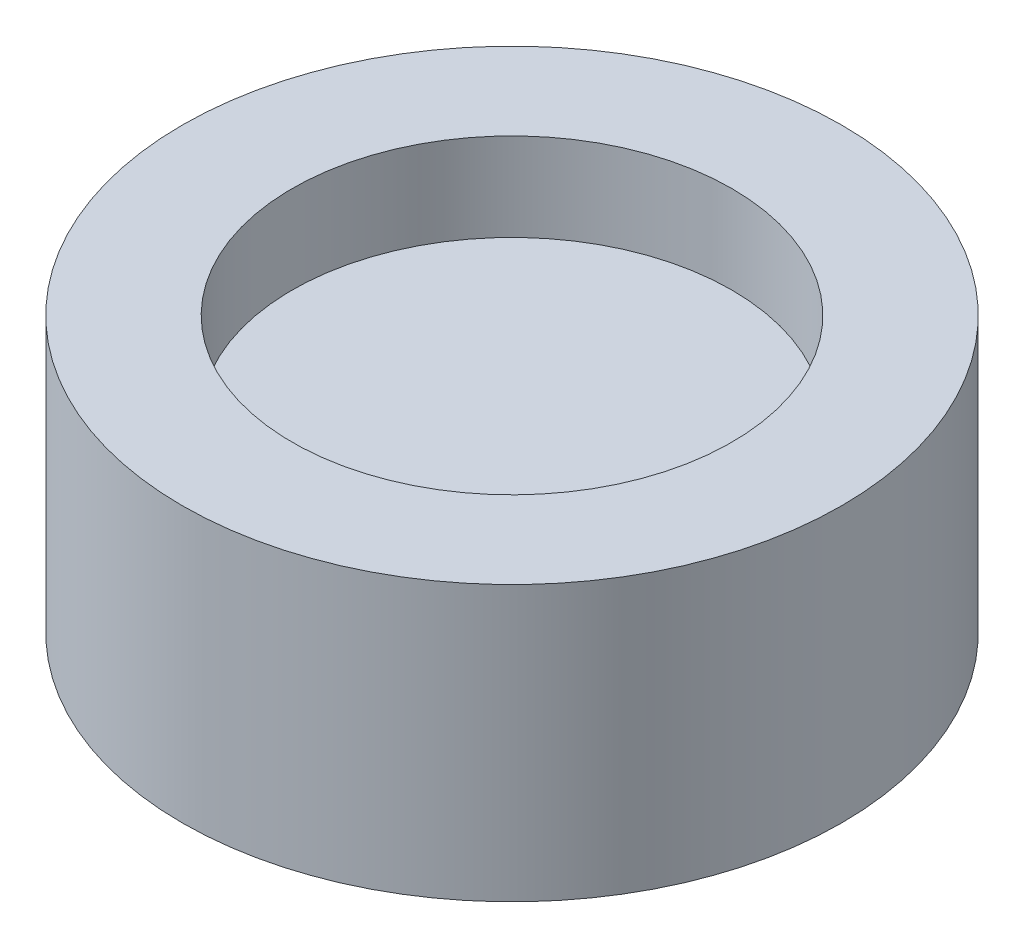
SolidWorks part; units mm, degrees
ref_plane "Plano frontal" through (0, 0, 0) normal (0, 0, 1) x (1, 0, 0)
ref_plane "Plano superior" through (0, 0, 0) normal (0, 1, 0) x (1, 0, 0)
ref_plane "Plano direito" through (0, 0, 0) normal (1, 0, 0) x (0, 0, -1)
sketch "Esboço1" plane through (0, 0, 0) normal (0, 0, 1) x (1, 0, 0)
  line L0 (0, 0) -> (0, 596.1298) construction
  line L1 (0, 0) -> (807.0529, 0) construction
  line L2 (200, 250) -> (300, 250)
  line L3 (300, 250) -> (300, 0)
  line L4 (300, 0) -> (0, 0)
  line L5 (0, 170) -> (0, 0)
  line L6 (200, 250) -> (200, 170)
  line L7 (200, 170) -> (0, 170)
  dimension "D1" = 600
  dimension "D2" = 250
  dimension "D3" = 80
  dimension "D4" = 400
revolve "Revolução1" add sketch "Esboço1" angle 360 about L0
sketch "Esboço2" plane through (0, 0, 0) normal (0, 0, 1) x (1, 0, 0)
  line L0 (0, 0) -> (0, 250) construction
  line L1 (200, 250) -> (-200, 250) construction
  line L2 (-50, 40) -> (50, 40)
  line L3 (50, 40) -> (50, 0)
  line L4 (-300, 0) -> (300, 0) construction
  line L5 (50, 0) -> (-50, 0)
  line L6 (-50, 40) -> (-50, 0)
  point P12 (0, 40)
  dimension "D1" = 100
  dimension "D2" = 40
extrude "Corte-extrusão1" [suppressed] cut sketch "Esboço2" against normal through all both and the other way through all
sketch "Esboço3" plane through (0, 0, 0) normal (0, -1, 0) x (1, 0, 0)
  line L1 (71, -55) -> (-71, -55) construction
  line L2 (71, -55) -> (71, 55) construction
  line L3 (71, 55) -> (-71, 55) construction
  line L4 (-71, -55) -> (-71, 55) construction
  line L5 (71, -55) -> (-71, 55) construction
  line L6 (71, 55) -> (-71, -55) construction
  circle A0 centre (-71, 55) radius 8
  circle A1 centre (71, 55) radius 8
  circle A2 centre (71, -55) radius 8
  circle A3 centre (-71, -55) radius 8
  point P0 (0, 0)
  dimension "D3" = 16
  dimension "D1" = 110
  dimension "D2" = 142
extrude "Corte-extrusão2" cut sketch "Esboço3" against normal blind 10
